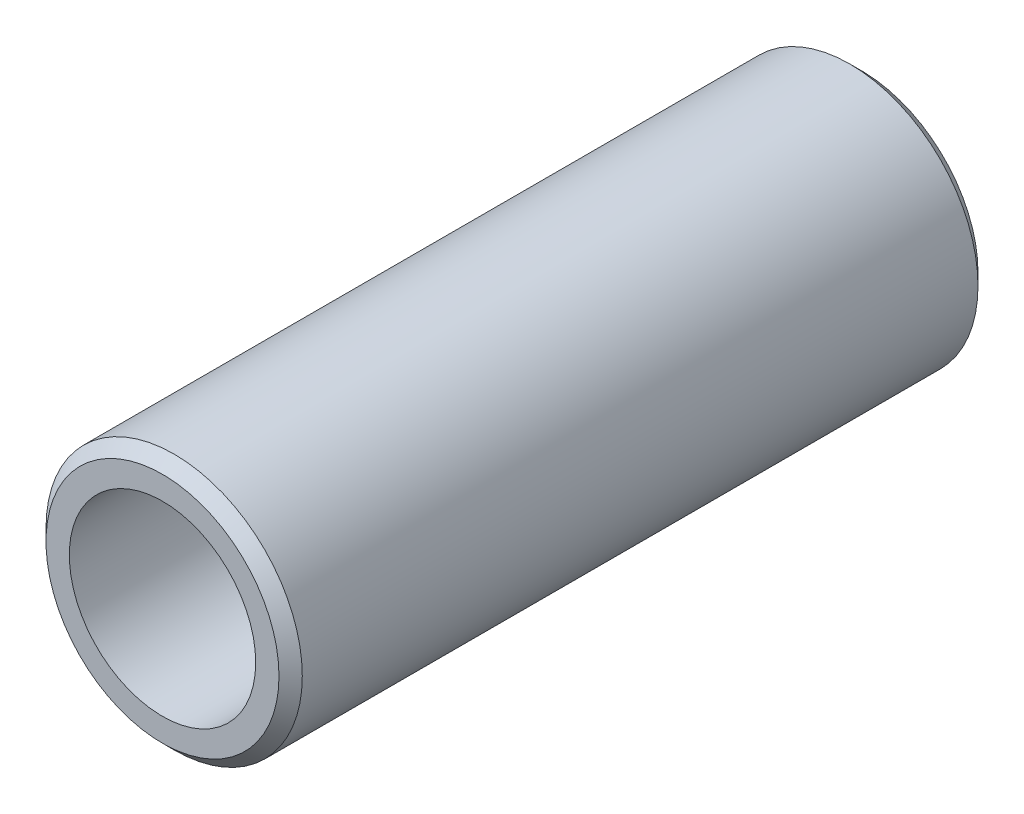
SolidWorks part; units mm, degrees
ref_plane "Piano frontale" through (0, 0, 0) normal (0, 0, 1) x (1, 0, 0)
ref_plane "Piano superiore" through (0, 0, 0) normal (0, 1, 0) x (1, 0, 0)
ref_plane "Piano destro" through (0, 0, 0) normal (1, 0, 0) x (0, 0, -1)
sketch "Schizzo1" plane through (0, 0, 0) normal (0, 0, 1) x (1, 0, 0)
  circle A0 centre (0, 0) radius 5.5
  dimension "D1" = 11
extrude "Estrusione-Estrusione1" add sketch "Schizzo1" along normal blind 30
sketch "Schizzo2" plane through (0, 0, 30) normal (0, 0, 1) x (1, 0, 0)
  circle A0 centre (0, 0) radius 4
  dimension "D1" = 8
extrude "Taglio-Estrusione1" cut sketch "Schizzo2" against normal through all
chamfer "Smusso1" distance 0.5 angle 45 2 edges at (5.5, 0, 0) (5.5, 0, 30)
